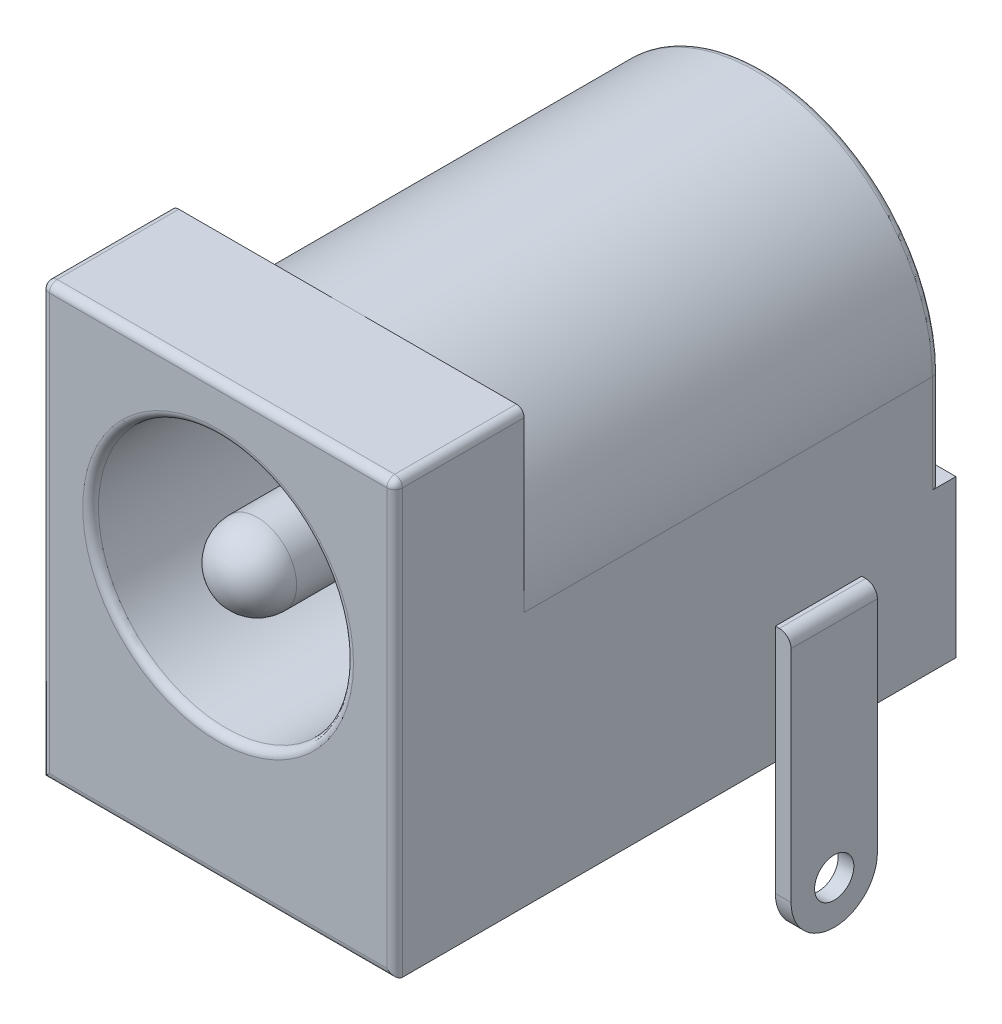
SolidWorks part; units mm, degrees
ref_plane "Front Plane" through (0, 0, 0) normal (0, 0, 1) x (1, 0, 0)
ref_plane "Top Plane" through (0, 0, 0) normal (0, 1, 0) x (1, 0, 0)
ref_plane "Right Plane" through (0, 0, 0) normal (1, 0, 0) x (0, 0, -1)
sketch "Sketch1" plane through (0, 0, 0) normal (0, 0, 1) x (1, 0, 0)
  line L1 (-4.5, 5.5) -> (4.5, 5.5)
  line L2 (-4.5, 5.5) -> (-4.5, -5.5)
  line L3 (-4.5, -5.5) -> (4.5, -5.5)
  line L4 (4.5, 5.5) -> (4.5, -5.5)
  line L5 (-4.5, 5.5) -> (4.5, -5.5) construction
  line L6 (-4.5, -5.5) -> (4.5, 5.5) construction
  point P0 (0, 0)
  dimension "D1" = 11
  dimension "D2" = 9
extrude "Boss-Extrude1" add sketch "Sketch1" against normal blind 3.3
sketch "Sketch2" plane through (0, 0, -3.3) normal (0, 0, -1) x (-1, 0, 0)
  line L0 (-4.5, -5.5) -> (4.5, -5.5)
  line L1 (4.5, -5.5) -> (4.5, 1)
  line L2 (4.5, 5.5) -> (4.5, -5.5) construction
  line L3 (-4.5, -5.5) -> (-4.5, 5.5) construction
  line L4 (-4.5, 1) -> (-4.5, -5.5)
  line L5 (-4.5, 5.5) -> (4.5, 5.5) construction
  arc A0 (4.5, 1) -> (-4.5, 1) centre (0, 1) ccw
extrude "Boss-Extrude2" add sketch "Sketch2" along normal blind 11
sketch "Sketch3" plane through (0, 0, 0) normal (0, 0, 1) x (1, 0, 0)
  line L0 (-4.5, -5.5) -> (4.5, -5.5) construction
  circle A0 centre (0, 1) radius 3.25
  dimension "D1" = 6.5
  dimension "D2" = 6.5
extrude "Cut-Extrude1" cut sketch "Sketch3" against normal blind 11
sketch "Sketch4" plane through (0, 0, -11) normal (0, 0, 1) x (1, 0, 0)
  circle A0 centre (0, 1) radius 1
  circle A1 centre (0, 1) radius 3.25 construction
  dimension "D1" = 2
extrude "Boss-Extrude3" add sketch "Sketch4" along normal blind 11
fillet "Fillet1" radius 1 1 edges at (1, 1, 0)
fillet "Fillet2" radius 0.2 7 edges at (0, -5.5, 0) (-4.5, 0, 0) (0, 5.5, 0) (4.5, 0, 0) (3.25, 1, 0) (-4.5, 5.5, -1.65) (4.5, 5.5, -1.65)
sketch "Sketch5" plane through (0, 0, -14.3) normal (0, 0, -1) x (-1, 0, 0)
  line L0 (4.5, -5.5) -> (4.5, 1) construction
  line L1 (4.5, -1.5) -> (1.2, -1.5)
  line L2 (4.5, -1.5) -> (4.5, 5.5)
  line L3 (4.5, 5.5) -> (-4.5, 5.5)
  line L4 (-4.5, -1.5) -> (-4.5, 5.5)
  line L5 (-4.5, 1) -> (-4.5, -5.5) construction
  line L6 (-1.2, -1.5) -> (-1.2, -5.5)
  line L7 (-4.5, -5.5) -> (4.5, -5.5) construction
  line L8 (-1.2, -5.5) -> (1.2, -5.5)
  line L9 (1.2, -5.5) -> (1.2, -1.5)
  line L10 (-1.2, -1.5) -> (-4.5, -1.5)
  arc A0 (4.5, 1) -> (-4.5, 1) centre (0, 1) ccw construction
  dimension "D1" = 2.4
  dimension "D2" = 4
extrude "Cut-Extrude2" cut sketch "Sketch5" against normal blind 0.4
sketch "Sketch6" plane through (0, 0, -13.9) normal (0, 0, -1) x (-1, 0, 0)
  line L0 (0, -8.4) -> (0, 1) construction
  line L1 (-1.1, -8.4) -> (-1.1, 1)
  line L2 (1.1, -8.4) -> (1.1, 1)
  line L3 (1.2, -5.5) -> (4.5, -5.5) construction
  arc A0 (-1.1, -8.4) -> (1.1, -8.4) centre (0, -8.4) ccw
  arc A1 (1.1, 1) -> (-1.1, 1) centre (0, 1) ccw
  arc A2 (4.5, 1) -> (-4.5, 1) centre (0, 1) ccw construction
  circle A3 centre (0, -8.4) radius 0.5
  circle A4 centre (0, 1) radius 0.5
  point P3 (0, -3.7)
  point P13 (0, -9.5)
  dimension "D1" = 1.1
  dimension "D3" = 1
  dimension "D2" = 4
extrude "Boss-Extrude4" add sketch "Sketch6" along normal blind 0.4
sketch "Sketch7" plane through (0, 0, -14.3) normal (0, 0, -1) x (-1, 0, 0)
  circle A0 centre (0, 1) radius 1.9
  circle A1 centre (0, 1) radius 0.5
  dimension "D1" = 3.8
extrude "Boss-Extrude5" add sketch "Sketch7" against normal blind 0.4
ref_plane "Plane1" through (0, 0, -8.1) normal (0, 0, -1) x (-1, 0, 0)
sketch "Sketch8" plane through (0, 0, -8.1) normal (0, 0, -1) x (-1, 0, 0)
  line L0 (-1.1, -5.1452) -> (-1.1, -8.4)
  line L1 (1.1, -8.4) -> (1.1, -5.1452)
  line L2 (1.1, -5.1452) -> (-1.1, -5.1452)
  line L3 (1.1, -8.4) -> (1.1, -0.5492) construction
  arc A0 (-1.1, -8.4) -> (1.1, -8.4) centre (0, -8.4) ccw
  circle A1 centre (0, -8.4) radius 0.5
  circle A2 centre (0, -8.4) radius 0.5 construction
  arc A3 (-1.1, -8.4) -> (1.1, -8.4) centre (0, -8.4) ccw construction
extrude "Boss-Extrude6" add sketch "Sketch8" against normal blind 0.4
sketch "Sketch9" plane through (4.5, 0, 0) normal (1, 0, 0) x (0, 0, -1)
  line L0 (9.7, -2.5) -> (9.7, -8.4)
  line L1 (11.9, -8.4) -> (11.9, -2.5)
  line L2 (11.9, -2.5) -> (9.7, -2.5)
  line L3 (13.9, -9.5) -> (14.3, -9.5) construction
  line L4 (7.9, -9.5) -> (14.1, -9.5) construction
  line L5 (7.7, -9.5) -> (8.1, -9.5) construction
  line L6 (0, -5.3) -> (0, 5.3) construction
  line L7 (14.3, -5.5) -> (0.2, -5.5) construction
  arc A0 (9.7, -8.4) -> (11.9, -8.4) centre (10.8, -8.4) ccw
  circle A1 centre (10.8, -8.4) radius 0.5
  point P5 (10.8, -9.5)
  dimension "D1" = 1
  dimension "D2" = 1.1
  dimension "D3" = 10.8
  dimension "D4" = 3
extrude "Boss-Extrude7" add sketch "Sketch9" along normal blind 0.4
sketch "Sketch10" plane through (0, 0, -11) normal (0, 0, 1) x (1, 0, 0)
  line L1 (-1.4, -2.75) -> (1.4, -2.75)
  line L2 (-1.4, -2.75) -> (-1.4, -1.75)
  line L3 (-1.4, -1.75) -> (1.4, -1.75)
  line L4 (1.4, -2.75) -> (1.4, -1.75)
  line L5 (-1.4, -2.75) -> (1.4, -1.75) construction
  line L6 (-1.4, -1.75) -> (1.4, -2.75) construction
  circle A0 centre (0, 1) radius 3.25 construction
  point P0 (0, -2.25)
  dimension "D1" = 2.8
  dimension "D2" = 0.5
extrude "Boss-Extrude8" add sketch "Sketch10" along normal blind 6.4
fillet "Fillet3" radius 0.3 2 edges at (4.9, -2.5, -10.8) (0, -1.75, -4.6)
fillet "Fillet4" radius 0.2 3 edges at (-4.5, -0.25, -13.9) (4.5, -0.25, -13.9) (0, 5.5, -13.9)
